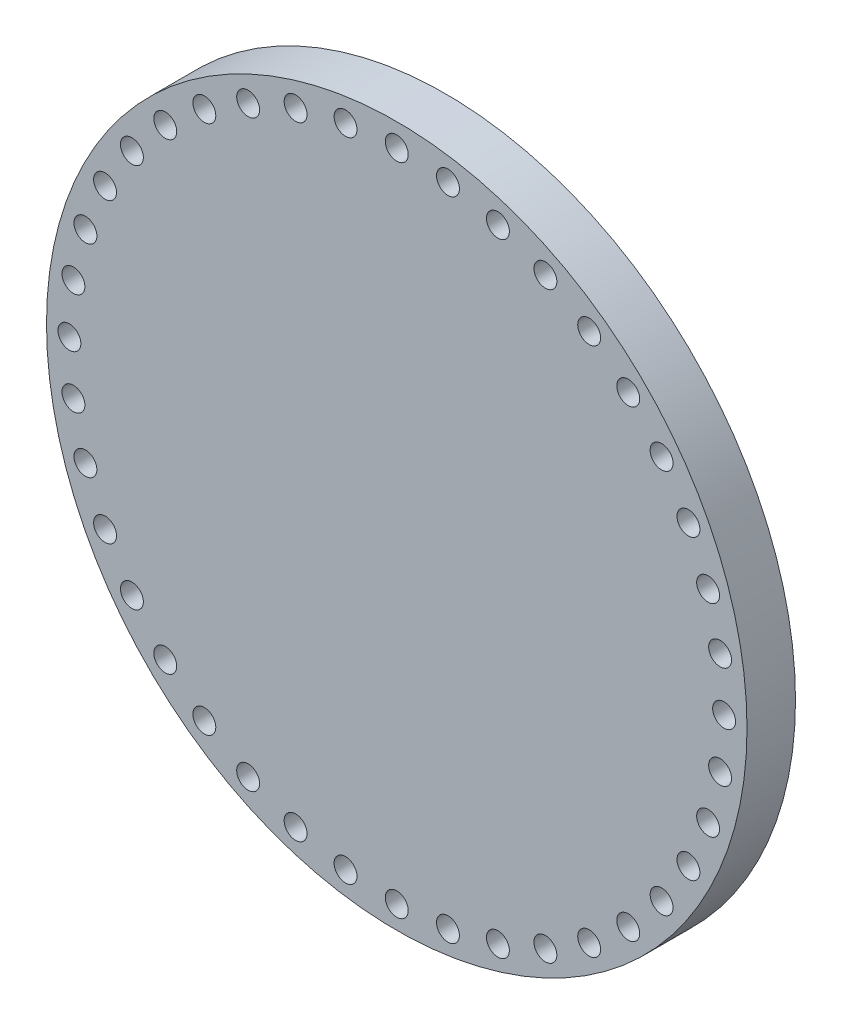
SolidWorks part; units mm, degrees
ref_plane "Front Plane" through (0, 0, 0) normal (0, 0, 1) x (1, 0, 0)
ref_plane "Top Plane" through (0, 0, 0) normal (0, 1, 0) x (1, 0, 0)
ref_plane "Right Plane" through (0, 0, 0) normal (1, 0, 0) x (0, 0, -1)
sketch "Sketch1" plane through (0, 0, 0) normal (0, 0, 1) x (1, 0, 0)
  circle A0 centre (0, 0) radius 32.5
  circle A2 centre (0, 30.375) radius 1.0625
  circle A3 centre (4.7517, 30.001) radius 1.0625
  circle A4 centre (9.3864, 28.8883) radius 1.0625
  circle A5 centre (13.79, 27.0643) radius 1.0625
  circle A6 centre (17.854, 24.5739) radius 1.0625
  circle A7 centre (21.4784, 21.4784) radius 1.0625
  circle A8 centre (24.5739, 17.854) radius 1.0625
  circle A9 centre (27.0643, 13.79) radius 1.0625
  circle A10 centre (28.8883, 9.3864) radius 1.0625
  circle A11 centre (30.001, 4.7517) radius 1.0625
  circle A12 centre (30.375, 0) radius 1.0625
  circle A13 centre (30.001, -4.7517) radius 1.0625
  circle A14 centre (28.8883, -9.3864) radius 1.0625
  circle A15 centre (27.0643, -13.79) radius 1.0625
  circle A16 centre (24.5739, -17.854) radius 1.0625
  circle A17 centre (21.4784, -21.4784) radius 1.0625
  circle A18 centre (17.854, -24.5739) radius 1.0625
  circle A19 centre (13.79, -27.0643) radius 1.0625
  circle A20 centre (9.3864, -28.8883) radius 1.0625
  circle A21 centre (4.7517, -30.001) radius 1.0625
  circle A22 centre (0, -30.375) radius 1.0625
  circle A23 centre (-4.7517, -30.001) radius 1.0625
  circle A24 centre (-9.3864, -28.8883) radius 1.0625
  circle A25 centre (-13.79, -27.0643) radius 1.0625
  circle A26 centre (-17.854, -24.5739) radius 1.0625
  circle A27 centre (-21.4784, -21.4784) radius 1.0625
  circle A28 centre (-24.5739, -17.854) radius 1.0625
  circle A29 centre (-27.0643, -13.79) radius 1.0625
  circle A30 centre (-28.8883, -9.3864) radius 1.0625
  circle A31 centre (-30.001, -4.7517) radius 1.0625
  circle A32 centre (-30.375, 0) radius 1.0625
  circle A33 centre (-30.001, 4.7517) radius 1.0625
  circle A34 centre (-28.8883, 9.3864) radius 1.0625
  circle A35 centre (-27.0643, 13.79) radius 1.0625
  circle A36 centre (-24.5739, 17.854) radius 1.0625
  circle A37 centre (-21.4784, 21.4784) radius 1.0625
  circle A38 centre (-17.854, 24.5739) radius 1.0625
  circle A39 centre (-13.79, 27.0643) radius 1.0625
  circle A40 centre (-9.3864, 28.8883) radius 1.0625
  circle A41 centre (-4.7517, 30.001) radius 1.0625
  point P85 (0, 0)
  dimension "D1" = 40
  dimension "D2" = 2.125
  dimension "D3" = 21.4784
  dimension "D15" = 65
extrude "Boss-Extrude1" add sketch "Sketch1" along normal blind 4.5
scale "Scale1" scale about centroid uniform scaling yes scale factor 25.4
